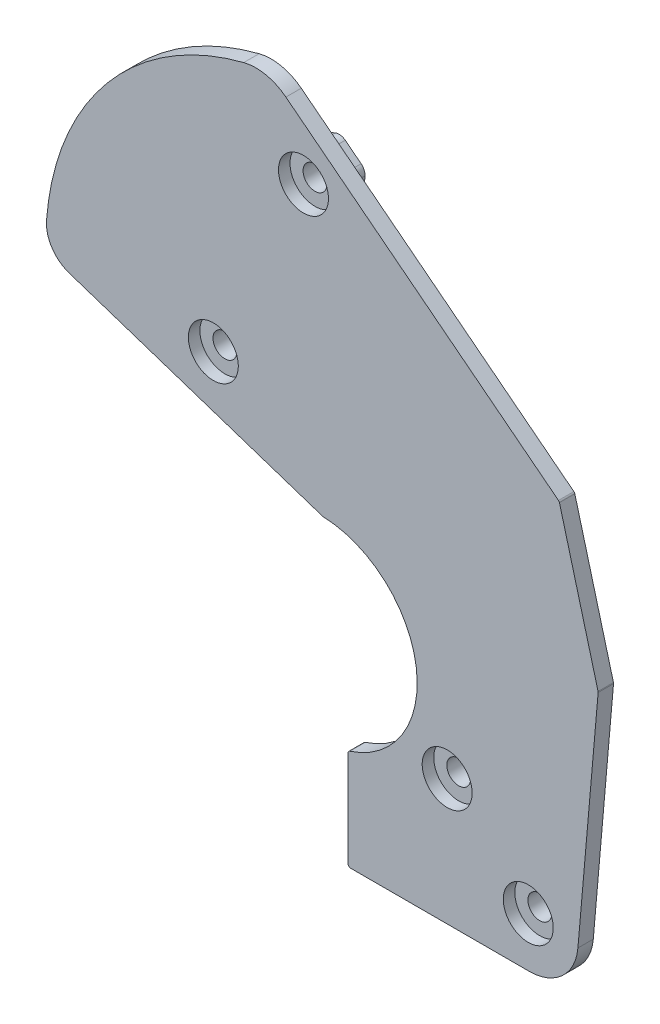
SolidWorks part; units mm, degrees
ref_plane "Ön Düzlem" through (0, 0, 0) normal (0, 0, 1) x (1, 0, 0)
ref_plane "Üst Düzlem" through (0, 0, 0) normal (0, 1, 0) x (1, 0, 0)
ref_plane "Sağ Düzlem" through (0, 0, 0) normal (1, 0, 0) x (0, 0, -1)
sketch "Çizim1" plane through (0, 0, 0) normal (0, 0, 1) x (1, 0, 0)
  line L6 (-41.1522, 11.1572) -> (-8.1403, 0.2294) construction
  line L7 (-5.0163, -24.6369) -> (-5.0163, -37.0832) construction
  line L8 (-4.5163, -37.5832) -> (18.7197, -37.5832) construction
  line L9 (25.1949, -31.6497) -> (27.828, -1.5541) construction
  line L10 (27.8128, -1.3811) -> (22.7874, 17.3741) construction
  line L11 (22.6122, 17.6387) -> (-12.8482, 45.3435) construction
  line L12 (-41.1051, 11.2996) -> (-8.1139, 0.3786)
  line L13 (-4.8663, -24.6369) -> (-4.8663, -37.0832)
  line L14 (-4.5163, -37.4332) -> (18.7197, -37.4332)
  line L15 (25.0455, -31.6366) -> (27.6785, -1.5411)
  line L16 (27.6679, -1.42) -> (22.6425, 17.3353)
  line L17 (22.5199, 17.5205) -> (-12.9406, 45.2253)
  arc A9 (-4.6699, -24.1611) -> (-8.1403, 0.2294) centre (-8.509, -12.2652) ccw construction
  arc A10 (-4.6699, -24.1611) -> (-5.0163, -24.6369) centre (-4.5163, -24.6369) ccw construction
  arc A11 (-5.0163, -37.0832) -> (-4.5163, -37.5832) centre (-4.5163, -37.0832) ccw construction
  arc A12 (18.7197, -37.5832) -> (25.1949, -31.6497) centre (18.7197, -31.0832) ccw construction
  arc A13 (27.828, -1.5541) -> (27.8128, -1.3811) centre (27.3299, -1.5105) ccw construction
  arc A14 (22.7874, 17.3741) -> (22.6122, 17.6387) centre (22.3044, 17.2447) ccw construction
  arc A15 (-12.8482, 45.3435) -> (-18.4614, 46.5185) centre (-16.85, 40.2214) ccw construction
  arc A16 (-44.2256, 15.7636) -> (-41.1522, 11.1572) centre (-39.7381, 15.4293) ccw construction
  arc A17 (-18.4614, 46.5185) -> (-44.2256, 15.7636) centre (-9.9379, 13.209) ccw construction
  arc A18 (-4.6238, -24.3038) -> (-8.1139, 0.3786) centre (-8.509, -12.2652) ccw
  arc A19 (-4.6238, -24.3038) -> (-4.8663, -24.6369) centre (-4.5163, -24.6369) ccw
  arc A20 (-4.8663, -37.0832) -> (-4.5163, -37.4332) centre (-4.5163, -37.0832) ccw
  arc A21 (18.7197, -37.4332) -> (25.0455, -31.6366) centre (18.7197, -31.0832) ccw
  arc A22 (27.6785, -1.5411) -> (27.6679, -1.42) centre (27.3299, -1.5105) ccw
  arc A23 (22.6425, 17.3353) -> (22.5199, 17.5205) centre (22.3044, 17.2447) ccw
  arc A24 (-12.9406, 45.2253) -> (-18.4242, 46.3732) centre (-16.85, 40.2214) ccw
  arc A25 (-18.4242, 46.3732) -> (-44.076, 15.7525) centre (-9.9379, 13.209) ccw
  arc A26 (-44.076, 15.7525) -> (-41.1051, 11.2996) centre (-39.7381, 15.4293) ccw
  dimension "D1" = 0.15
extrude "Yükseklik-Ekstrüzyon1" add sketch "Çizim1" against normal blind 2
sketch "Çizim4" plane through (0, 0, -2) normal (0, 0, -1) x (-1, 0, 0)
  line L19 (40.2094, 14.0053) -> (28.5369, 10.1413) construction
  line L20 (8.2951, 3.4407) -> (28.5369, 10.1413) construction
  line L21 (5.6429, 4.5372) -> (6.9781, 3.6258) construction
  line L22 (-6.4948, -17.7353) -> (-7.6212, -17.2934) construction
  line L23 (0.6372, -25.6176) -> (0.6372, -34.5832) construction
  line L24 (0.6372, -34.5832) -> (-5.1272, -34.5832) construction
  line L25 (-6.3961, -33.8832) -> (-6.7807, -33.8832) construction
  line L26 (-6.7807, -33.8832) -> (-14.9835, -33.8832) construction
  line L27 (-14.9835, -33.8832) -> (-18.7197, -33.8832) construction
  line L28 (-21.509, -31.3272) -> (-21.6061, -30.2171) construction
  line L29 (-21.3654, -29.2625) -> (-20.7861, -28.381) construction
  line L30 (-20.5453, -27.4265) -> (-20.5727, -27.1141) construction
  line L31 (-20.5727, -27.1141) -> (-22.7548, -2.1723) construction
  line L32 (-22.7094, -1.6533) -> (-18.4773, 14.1409) construction
  line L33 (-17.952, 14.9346) -> (6.9362, 34.3794) construction
  line L34 (7.4531, 36.4848) -> (7.5092, 35.6636) construction
  line L35 (10.0932, 39.3839) -> (8.0261, 37.769) construction
  line L36 (11.5985, 39.5845) -> (12.0868, 39.379) construction
  line L37 (13.5921, 39.5796) -> (15.9265, 41.4034) construction
  line L38 (0.0163, -25.2315) -> (-0.3556, -24.9801) construction
  line L39 (40.1466, 14.1951) -> (28.4741, 10.3312)
  line L40 (8.2323, 3.6306) -> (28.4741, 10.3312)
  line L41 (5.7557, 4.7024) -> (7.0908, 3.791)
  line L42 (-6.5678, -17.9214) -> (-7.6942, -17.4796)
  line L43 (-0.0945, -25.398) -> (-0.4688, -25.145)
  line L44 (0.4372, -25.7313) -> (0.4372, -34.3832)
  line L45 (0.4372, -34.3832) -> (-5.0213, -34.3832)
  line L46 (-6.3961, -33.6832) -> (-6.7807, -33.6832)
  line L47 (-6.7807, -33.6832) -> (-14.9835, -33.6832)
  line L48 (-14.9835, -33.6832) -> (-18.7197, -33.6832)
  line L49 (-21.3098, -31.3098) -> (-21.4069, -30.1997)
  line L50 (-21.1983, -29.3724) -> (-20.6189, -28.4909)
  line L51 (-20.3461, -27.4091) -> (-20.3734, -27.0967)
  line L52 (-20.3734, -27.0967) -> (-22.5555, -2.1549)
  line L53 (-22.5162, -1.7051) -> (-18.2842, 14.0891)
  line L54 (-17.8288, 14.777) -> (7.0593, 34.2218)
  line L55 (7.6526, 36.4984) -> (7.7087, 35.6772)
  line L56 (10.2163, 39.2263) -> (8.1493, 37.6114)
  line L57 (11.521, 39.4001) -> (12.0092, 39.1947)
  line L58 (13.7152, 39.422) -> (16.0497, 41.2458)
  line L59 (20.9718, 41.5445) -> (20.7423, 41.3247)
  line L60 (20.8334, 41.689) -> (20.604, 41.4692) construction
  arc A26 (40.2094, 14.0053) -> (41.2339, 15.5407) centre (39.7381, 15.4293) ccw construction
  arc A27 (6.9781, 3.6258) -> (8.2951, 3.4407) centre (7.8237, 4.8647) ccw construction
  arc A28 (5.6429, 4.5372) -> (4.4493, 4.7574) centre (4.7973, 3.2983) ccw construction
  arc A29 (4.4493, 4.7574) -> (3.8607, 4.6062) centre (8.509, -12.2652) ccw construction
  arc A30 (3.8607, 4.6062) -> (-8.7804, -14.9718) centre (8.509, -12.2652) ccw construction
  arc A31 (-8.7804, -14.9718) -> (-8.5342, -16.2375) centre (8.509, -12.2652) ccw construction
  arc A32 (-8.5342, -16.2375) -> (-7.6212, -17.2934) centre (-7.0734, -15.897) ccw construction
  arc A33 (-5.6704, -18.5258) -> (-6.4948, -17.7353) centre (-7.0426, -19.1316) ccw construction
  arc A34 (-5.6704, -18.5258) -> (-0.3556, -24.9801) centre (8.509, -12.2652) ccw construction
  arc A35 (0.0163, -25.2315) -> (0.6372, -25.6176) centre (8.509, -12.2652) ccw construction
  arc A36 (-5.1272, -34.5832) -> (-6.3961, -33.8832) centre (-6.3961, -35.3832) ccw construction
  arc A37 (-21.509, -31.3272) -> (-18.7197, -33.8832) centre (-18.7197, -31.0832) ccw construction
  arc A38 (-21.3654, -29.2625) -> (-21.6061, -30.2171) centre (-20.1119, -30.0864) ccw construction
  arc A39 (-20.7861, -28.381) -> (-20.5453, -27.4265) centre (-22.0396, -27.5572) ccw construction
  arc A40 (-22.7094, -1.6533) -> (-22.7548, -2.1723) centre (-21.2605, -2.0415) ccw construction
  arc A41 (-17.952, 14.9346) -> (-18.4773, 14.1409) centre (-17.0285, 13.7526) ccw construction
  arc A42 (6.9362, 34.3794) -> (7.4227, 35.0496) centre (6.0127, 35.5614) ccw construction
  arc A43 (7.4227, 35.0496) -> (7.5092, 35.6636) centre (6.0127, 35.5614) ccw construction
  arc A44 (8.0261, 37.769) -> (7.4531, 36.4848) centre (8.9496, 36.587) ccw construction
  arc A45 (11.5985, 39.5845) -> (10.0932, 39.3839) centre (11.0167, 38.2019) ccw construction
  arc A46 (12.0868, 39.379) -> (13.5921, 39.5796) centre (12.6686, 40.7616) ccw construction
  arc A47 (17.2219, 41.6746) -> (15.9265, 41.4034) centre (16.85, 40.2214) ccw construction
  arc A48 (19.0987, 41.1272) -> (17.2219, 41.6746) centre (9.9379, 13.209) ccw construction
  arc A49 (19.0987, 41.1272) -> (20.604, 41.4692) centre (19.5664, 42.5524) ccw construction
  arc A50 (22.47, 41.9809) -> (20.8334, 41.689) centre (21.871, 40.6057) ccw construction
  arc A51 (41.2339, 15.5407) -> (22.47, 41.9809) centre (9.9379, 13.209) ccw construction
  arc A52 (22.3901, 41.7976) -> (20.9718, 41.5445) centre (21.871, 40.6057) ccw
  arc A53 (41.0345, 15.5258) -> (22.3901, 41.7976) centre (9.9379, 13.209) ccw
  arc A54 (40.1466, 14.1951) -> (41.0345, 15.5258) centre (39.7381, 15.4293) ccw
  arc A55 (7.0908, 3.791) -> (8.2323, 3.6306) centre (7.8237, 4.8647) ccw
  arc A56 (5.7557, 4.7024) -> (4.4029, 4.9519) centre (4.7973, 3.2983) ccw
  arc A57 (4.4029, 4.9519) -> (3.8076, 4.799) centre (8.509, -12.2652) ccw
  arc A58 (3.8076, 4.799) -> (-8.978, -15.0027) centre (8.509, -12.2652) ccw
  arc A59 (-8.978, -15.0027) -> (-8.729, -16.2829) centre (8.509, -12.2652) ccw
  arc A60 (-8.729, -16.2829) -> (-7.6942, -17.4796) centre (-7.0734, -15.897) ccw
  arc A61 (-5.8534, -18.6066) -> (-6.5678, -17.9214) centre (-7.0426, -19.1316) ccw
  arc A62 (-5.8534, -18.6066) -> (-0.4688, -25.145) centre (8.509, -12.2652) ccw
  arc A63 (-0.0945, -25.398) -> (0.4372, -25.7313) centre (8.509, -12.2652) ccw
  arc A64 (-5.0213, -34.3832) -> (-6.3961, -33.6832) centre (-6.3961, -35.3832) ccw
  arc A65 (-21.3098, -31.3098) -> (-18.7197, -33.6832) centre (-18.7197, -31.0832) ccw
  arc A66 (-21.1983, -29.3724) -> (-21.4069, -30.1997) centre (-20.1119, -30.0864) ccw
  arc A67 (-20.6189, -28.4909) -> (-20.3461, -27.4091) centre (-22.0396, -27.5572) ccw
  arc A68 (-22.5162, -1.7051) -> (-22.5555, -2.1549) centre (-21.2605, -2.0415) ccw
  arc A69 (-17.8288, 14.777) -> (-18.2842, 14.0891) centre (-17.0285, 13.7526) ccw
  arc A70 (7.0593, 34.2218) -> (7.6107, 34.9813) centre (6.0127, 35.5614) ccw
  arc A71 (7.6107, 34.9813) -> (7.7087, 35.6772) centre (6.0127, 35.5614) ccw
  arc A72 (8.1493, 37.6114) -> (7.6526, 36.4984) centre (8.9496, 36.587) ccw
  arc A73 (11.521, 39.4001) -> (10.2163, 39.2263) centre (11.0167, 38.2019) ccw
  arc A74 (12.0092, 39.1947) -> (13.7152, 39.422) centre (12.6686, 40.7616) ccw
  arc A75 (17.1723, 41.4808) -> (16.0497, 41.2458) centre (16.85, 40.2214) ccw
  arc A76 (19.0364, 40.9372) -> (17.1723, 41.4808) centre (9.9379, 13.209) ccw
  arc A77 (19.0364, 40.9372) -> (20.7423, 41.3247) centre (19.5664, 42.5524) ccw
  dimension "D1" = 0.2
extrude "Yükseklik-Ekstrüzyon2" add sketch "Çizim4" along normal blind 3
sketch "Çizim5" plane through (0, 0, 0) normal (0, 0, 1) x (1, 0, 0)
  circle A0 centre (18.5883, -30.9881) radius 1.55
  circle A1 centre (8.0407, -21.0653) radius 1.55
  circle A2 centre (-22.3762, 11.8283) radius 1.55
  circle A3 centre (-10.6559, 36.5555) radius 1.55
extrude "Kes-Ekstrüzyon1" cut sketch "Çizim5" against normal up to surface (5 mm away) up to face at (-1.3728, 4.9096, -5)
sketch "Çizim6" plane through (0, 0, 0) normal (0, 0, 1) x (1, 0, 0)
  circle A0 centre (18.5883, -30.9881) radius 3.25
  circle A1 centre (8.0407, -21.0653) radius 3.25
  circle A2 centre (-22.3762, 11.8283) radius 3.25
  circle A3 centre (-10.6559, 36.5555) radius 3.25
extrude "Kes-Ekstrüzyon2" cut sketch "Çizim6" against normal blind 1.5
sketch "Çizim7" plane through (0, 0, -5) normal (0, 0, -1) x (-1, 0, 0)
  line L0 (24.5413, 38.1096) -> (23.5177, 39.204)
  line L5 (31.2203, 31.1986) -> (22.5986, 40.1999) construction
  line L7 (27.0669, 13.449) -> (14.8148, 26.5496)
  line L9 (38.3839, 23.3083) -> (24.5413, 38.1096)
  line L10 (28.2518, 12.1789) -> (24.2268, 38.5) construction
  line L11 (13.2531, 28.2737) -> (39.2254, 22.4053) construction
  line L12 (19.6347, 39.6323) -> (16.6112, 37.5674)
  line L13 (16.373, 37.3765) -> (11.6373, 32.9475)
  line L14 (11.5288, 30.1356) -> (14.8148, 26.5496)
  line L15 (38.9208, 22.0413) -> (39.0841, 18.7486)
  line L16 (33.4521, 12.8146) -> (28.5299, 12.8142)
  line L17 (35.6308, 13.7526) -> (38.2667, 16.5379)
  arc A8 (16.6112, 37.5674) -> (16.373, 37.3765) centre (17.7391, 35.9158) ccw
  arc A9 (11.6373, 32.9475) -> (11.5288, 30.1356) centre (13.0034, 31.4868) ccw
  arc A10 (38.3839, 23.3083) -> (38.9208, 22.0413) centre (36.9232, 21.9422) cw
  arc A12 (27.0669, 13.449) -> (28.5299, 12.8142) centre (28.5298, 14.8171) ccw
  arc A13 (39.0841, 18.7486) -> (38.2667, 16.5379) centre (36.0878, 18.5999) cw
  arc A14 (33.4521, 12.8146) -> (35.6308, 13.7526) centre (33.4519, 15.8146) ccw
  arc A15 (19.6347, 39.6323) -> (23.5177, 39.204) centre (21.3266, 37.1549) cw
  point P0 (26.2393, 25.3395)
  dimension "D3" = 3
  dimension "D1" = 2
  dimension "D4" = 3
  dimension "D2" = 15
extrude "Kes-Ekstrüzyon3" cut sketch "Çizim7" against normal blind 2
